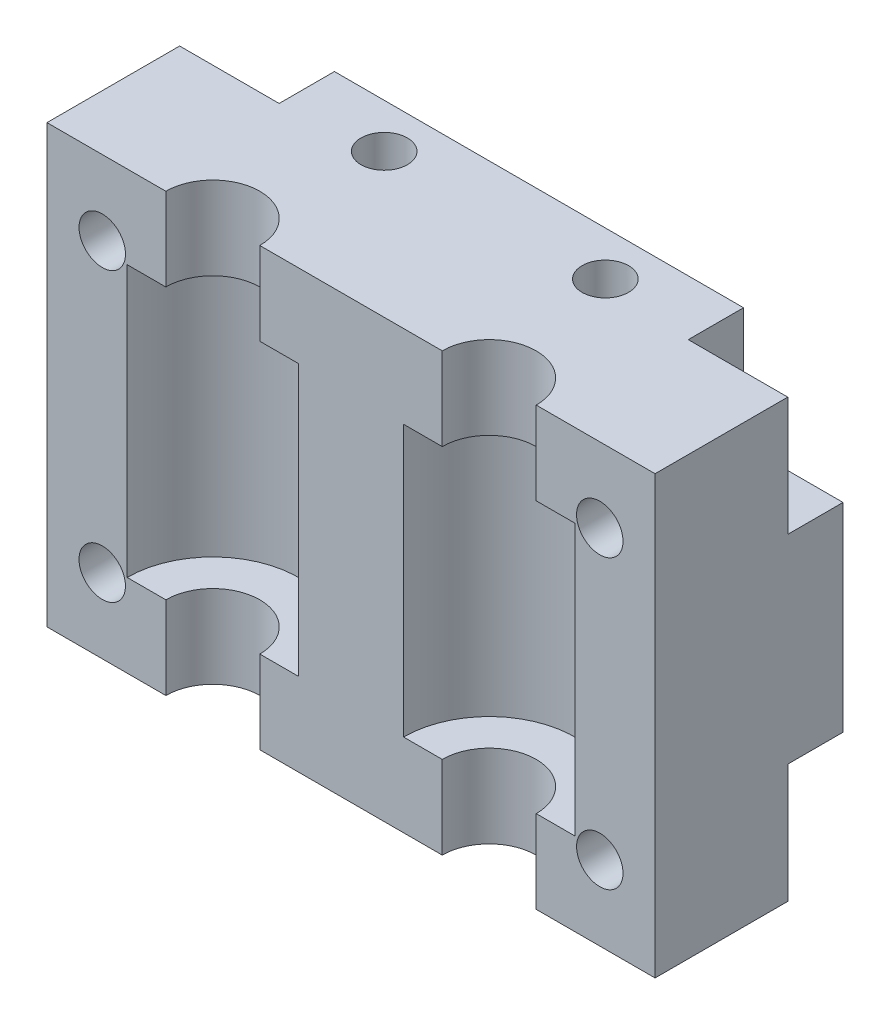
SolidWorks part; units mm, degrees
ref_plane "Plan de face" through (0, 0, 0) normal (0, 0, 1) x (1, 0, 0)
ref_plane "Plan de dessus" through (0, 0, 0) normal (0, 1, 0) x (1, 0, 0)
ref_plane "Plan de droite" through (0, 0, 0) normal (1, 0, 0) x (0, 0, -1)
sketch "Esquisse1" plane through (0, 0, 0) normal (0, 0, 1) x (1, 0, 0)
  line L1 (-27.5, -22.5) -> (27.5, -22.5)
  line L2 (-27.5, -22.5) -> (-27.5, 22.5)
  line L3 (-27.5, 22.5) -> (27.5, 22.5)
  line L4 (27.5, -22.5) -> (27.5, 22.5)
  line L5 (-27.5, -22.5) -> (27.5, 22.5) construction
  line L6 (-27.5, 22.5) -> (27.5, -22.5) construction
  point P0 (0, 0)
  dimension "D1" = 55
  dimension "D2" = 45
extrude "Boss.-Extru.1" add sketch "Esquisse1" along normal blind 12
sketch "Esquisse2" plane through (0, 22.5, 0) normal (0, 1, 0) x (1, 0, 0)
  line L0 (27.5, -12) -> (-27.5, -12) construction
  line L1 (-27.5, -12) -> (-27.5, 0) construction
  line L2 (27.5, -12) -> (27.5, 0) construction
  circle A0 centre (-12.5, -12) radius 4.25
  circle A1 centre (12.5, -12) radius 4.25
  dimension "D1" = 8.5
  dimension "D3" = 8.5
  dimension "D2" = 15
  dimension "D4" = 15
extrude "Enlèv. mat.-Extru.1" cut sketch "Esquisse2" against normal through all
sketch "Esquisse3" plane through (0, 0, 0) normal (0, 1, 0) x (1, 0, 0)
  circle A0 centre (-12.5, -12) radius 7.75
  dimension "D1" = 15.5
extrude "Enlèv. mat.-Extru.2" cut sketch "Esquisse3" against normal blind 12.25 and the other way blind 12.25
sketch "Esquisse9" plane through (0, 0, 12) normal (0, 0, 1) x (1, 0, 0)
  line L0 (-8.25, -22.5) -> (8.25, -22.5) construction
  line L1 (-30.9208, -30.2281) -> (30.1419, -30.2281)
  line L2 (-30.9208, -30.2281) -> (-30.9208, -18)
  line L3 (-30.9208, -18) -> (30.1419, -18)
  line L4 (30.1419, -30.2281) -> (30.1419, -18)
  line L5 (8.25, 22.5) -> (-8.25, 22.5) construction
  line L6 (31.3881, 26.1002) -> (-28.039, 26.1002)
  line L7 (31.3881, 26.1002) -> (31.3881, 18)
  line L8 (31.3881, 18) -> (-28.039, 18)
  line L9 (-28.039, 26.1002) -> (-28.039, 18)
  dimension "D1" = 4.5
  dimension "D2" = 4.5
extrude "Enlèv. mat.-Extru.7" cut sketch "Esquisse9" against normal blind 31
sketch "Sketch1" plane through (0, 0, 0) normal (0, 0, -1) x (-1, 0, 0)
  line L4 (-27.5, -18) -> (27.5, -18)
  line L5 (27.5, -18) -> (27.5, 18)
  line L6 (27.5, 18) -> (-27.5, 18)
  line L7 (-27.5, 18) -> (-27.5, -18)
  line L8 (-27.5, -18) -> (27.5, -18)
  line L9 (27.5, -18) -> (27.5, 18)
  line L10 (27.5, 18) -> (-27.5, 18)
  line L11 (-27.5, 18) -> (-27.5, -18)
  dimension "D1" = 0
extrude "Boss-Extrude1" add sketch "Sketch1" along normal blind 5
sketch "Sketch2" plane through (0, 0, 12) normal (0, 0, 1) x (1, 0, 0)
  line L0 (-27.5, 18) -> (-16.75, 18) construction
  line L1 (-27.5, 18) -> (-27.5, -18) construction
  line L2 (0, 18) -> (0, -18) construction
  line L3 (-8.25, 18) -> (8.25, 18) construction
  line L4 (8.25, -18) -> (-8.25, -18) construction
  line L5 (-27.5, 0) -> (27.5, 0) construction
  line L6 (27.5, -18) -> (27.5, 18) construction
  circle A0 centre (-22.5, 13) radius 2.1
  circle A1 centre (22.5, 13) radius 2.1
  circle A2 centre (22.5, -13) radius 2.1
  circle A3 centre (-22.5, -13) radius 2.1
  dimension "D1" = 4.2
  dimension "D2" = 5
  dimension "D3" = 5
extrude "Cut-Extrude1" cut sketch "Sketch2" against normal through all
sketch "Sketch3" plane through (0, 0, -5) normal (0, 0, -1) x (-1, 0, 0)
  circle A0 centre (-22.5, 13) radius 4
  circle A1 centre (22.5, 13) radius 4
  circle A2 centre (22.5, -13) radius 4
  circle A3 centre (-22.5, -13) radius 4
  dimension "D1" = 8
extrude "Cut-Extrude2" cut sketch "Sketch3" against normal blind 10
sketch "Sketch4" plane through (0, 0, -5) normal (0, 0, -1) x (-1, 0, 0)
  line L0 (-18.5, 13) -> (-18.5, 18)
  line L1 (-22.5, 9) -> (-27.5, 9)
  line L2 (-22.5, -9) -> (-27.5, -9)
  line L3 (-18.5, -13) -> (-18.5, -18)
  line L4 (-27.5, 18) -> (-27.5, -18)
  line L5 (-27.5, -18) -> (27.5, -18)
  line L6 (27.5, -18) -> (27.5, 18)
  line L7 (27.5, 18) -> (-27.5, 18)
  line L8 (-27.5, 18) -> (-27.5, 9)
  line L9 (-27.5, -18) -> (-18.5, -18)
  line L10 (27.5, -18) -> (27.5, -9)
  line L11 (27.5, 18) -> (18.5, 18)
  line L12 (18.5, -13) -> (18.5, -18)
  line L13 (22.5, -9) -> (27.5, -9)
  line L14 (22.5, 9) -> (27.5, 9)
  line L15 (18.5, 13) -> (18.5, 18)
  line L16 (-18.5, 18) -> (-27.5, 18)
  line L17 (-27.5, -9) -> (-27.5, -18)
  line L18 (18.5, -18) -> (27.5, -18)
  line L19 (27.5, 9) -> (27.5, 18)
  circle A0 centre (-22.5, 13) radius 4 construction
  circle A1 centre (-22.5, -13) radius 4 construction
  circle A2 centre (22.5, -13) radius 4 construction
  circle A3 centre (22.5, 13) radius 4 construction
  arc A4 (-18.5, 13) -> (-22.5, 9) centre (-22.5, 13) ccw
  arc A5 (-22.5, -9) -> (-18.5, -13) centre (-22.5, -13) ccw
  arc A6 (18.5, -13) -> (22.5, -9) centre (22.5, -13) ccw
  arc A7 (22.5, 9) -> (18.5, 13) centre (22.5, 13) ccw
  dimension "D1" = 0
extrude "Cut-Extrude3" cut sketch "Sketch4" against normal blind 5
sketch "Sketch5" plane through (0, 18, 0) normal (0, 1, 0) x (1, 0, 0)
  line L0 (-27.5, -12) -> (-27.5, 0) construction
  line L1 (27.5, 0) -> (27.5, 5) construction
  line L2 (-18.5, 5) -> (18.5, 5) construction
  circle A0 centre (-10, 1) radius 2.1
  circle A1 centre (10, 1) radius 2.1
  dimension "D1" = 4.2
  dimension "D2" = 4.2
  dimension "D3" = 17.5
  dimension "D4" = 17.5
  dimension "D5" = 4
  dimension "D6" = 4
extrude "Cut-Extrude4" cut sketch "Sketch5" against normal through all
sketch "Sketch7" plane through (0, 18, 0) normal (0, 1, 0) x (1, 0, 0)
  line L10 (18.5, 5) -> (-18.5, 5)
  line L11 (-18.5, 5) -> (-18.5, 0)
  line L12 (-18.5, 0) -> (-27.5, 0)
  line L13 (-27.5, 0) -> (-27.5, -12)
  line L14 (-27.5, -12) -> (-16.75, -12)
  line L15 (-8.25, -12) -> (8.25, -12)
  line L16 (16.75, -12) -> (27.5, -12)
  line L17 (27.5, -12) -> (27.5, 0)
  line L18 (27.5, 0) -> (18.5, 0)
  line L19 (18.5, 0) -> (18.5, 5)
  line L20 (18.5, 5) -> (-18.5, 5)
  line L21 (-18.5, 5) -> (-18.5, 0)
  line L22 (-18.5, 0) -> (-27.5, 0)
  line L23 (-27.5, 0) -> (-27.5, -12)
  line L24 (-27.5, -12) -> (-16.75, -12)
  line L25 (-8.25, -12) -> (8.25, -12)
  line L26 (16.75, -12) -> (27.5, -12)
  line L27 (27.5, -12) -> (27.5, 0)
  line L28 (27.5, 0) -> (18.5, 0)
  line L29 (18.5, 0) -> (18.5, 5)
  circle A0 centre (10, 1) radius 2.1 construction
  circle A1 centre (-10, 1) radius 2.1 construction
  arc A2 (-8.25, -12) -> (-16.75, -12) centre (-12.5, -12) ccw
  arc A3 (16.75, -12) -> (8.25, -12) centre (12.5, -12) ccw
  arc A4 (-8.25, -12) -> (-16.75, -12) centre (-12.5, -12) ccw
  arc A5 (16.75, -12) -> (8.25, -12) centre (12.5, -12) ccw
  circle A6 centre (10, 1) radius 2.1
  circle A7 centre (-10, 1) radius 2.1
  dimension "D1" = 0
extrude "Boss-Extrude4" add sketch "Sketch7" along normal blind 2
sketch "Sketch8" plane through (0, -18, 0) normal (0, -1, 0) x (1, 0, 0)
  line L10 (-27.5, 0) -> (-18.5, 0)
  line L11 (-18.5, 0) -> (-18.5, -5)
  line L12 (-18.5, -5) -> (18.5, -5)
  line L13 (18.5, -5) -> (18.5, 0)
  line L14 (18.5, 0) -> (27.5, 0)
  line L15 (27.5, 0) -> (27.5, 12)
  line L16 (27.5, 12) -> (16.75, 12)
  line L17 (8.25, 12) -> (-8.25, 12)
  line L18 (-16.75, 12) -> (-27.5, 12)
  line L19 (-27.5, 12) -> (-27.5, 0)
  line L20 (-27.5, 0) -> (-18.5, 0)
  line L21 (-18.5, 0) -> (-18.5, -5)
  line L22 (-18.5, -5) -> (18.5, -5)
  line L23 (18.5, -5) -> (18.5, 0)
  line L24 (18.5, 0) -> (27.5, 0)
  line L25 (27.5, 0) -> (27.5, 12)
  line L26 (27.5, 12) -> (16.75, 12)
  line L27 (8.25, 12) -> (-8.25, 12)
  line L28 (-16.75, 12) -> (-27.5, 12)
  line L29 (-27.5, 12) -> (-27.5, 0)
  circle A0 centre (-10, -1) radius 2.1 construction
  circle A1 centre (10, -1) radius 2.1 construction
  arc A2 (8.25, 12) -> (16.75, 12) centre (12.5, 12) ccw
  arc A3 (-16.75, 12) -> (-8.25, 12) centre (-12.5, 12) ccw
  arc A4 (8.25, 12) -> (16.75, 12) centre (12.5, 12) ccw
  arc A5 (-16.75, 12) -> (-8.25, 12) centre (-12.5, 12) ccw
  circle A6 centre (10, -1) radius 2.1
  circle A7 centre (-10, -1) radius 2.1
  dimension "D1" = 0
extrude "Boss-Extrude5" add sketch "Sketch8" along normal blind 2
sketch "Sketch9" plane through (0, 0, -5) normal (0, 0, -1) x (-1, 0, 0)
  line L0 (-27.5, 20) -> (-27.5, 9) construction
  line L1 (-13.5, 16) -> (-6.5, 16)
  line L2 (-13.5, 16) -> (-13.5, 12.8)
  line L3 (-13.5, 12.8) -> (-6.5, 12.8)
  line L4 (-6.5, 16) -> (-6.5, 12.8)
  line L5 (-18.5, 20) -> (18.5, 20) construction
  line L6 (0, 20) -> (0, -9.1772) construction
  line L7 (13.5, 12.8) -> (6.5, 12.8)
  line L8 (6.5, 16) -> (6.5, 12.8)
  line L9 (13.5, 16) -> (6.5, 16)
  line L10 (13.5, 16) -> (13.5, 12.8)
  line L11 (-27.5, 0) -> (-8.3783, 0) construction
  line L12 (-27.5, 9) -> (-27.5, -9) construction
  line L13 (13.5, -16) -> (13.5, -12.8)
  line L14 (13.5, -16) -> (6.5, -16)
  line L15 (6.5, -16) -> (6.5, -12.8)
  line L16 (13.5, -12.8) -> (6.5, -12.8)
  line L17 (-13.5, -12.8) -> (-6.5, -12.8)
  line L18 (-6.5, -16) -> (-6.5, -12.8)
  line L19 (-13.5, -16) -> (-6.5, -16)
  line L20 (-13.5, -16) -> (-13.5, -12.8)
  point P4 (-10, 16)
  dimension "D1" = 7
  dimension "D2" = 17.5
  dimension "D3" = 4
  dimension "D4" = 3.2
extrude "Cut-Extrude6" cut sketch "Sketch9" against normal blind 8
ref_plane "Plane1" through (0, 0, 0) normal (-1, 0, 0) x (0, 0, 1)
mirror "Mirror1" about plane through (0, 0, 0) normal (-1, 0, 0) of "Enlèv. mat.-Extru.2"
sketch "Sketch10" plane through (0, -20, 0) normal (0, -1, 0) x (1, 0, 0)
  line L10 (-27.5, 12) -> (-27.5, 0)
  line L11 (-27.5, 0) -> (-18.5, 0)
  line L12 (-18.5, 0) -> (-18.5, -5)
  line L13 (-18.5, -5) -> (18.5, -5)
  line L14 (18.5, -5) -> (18.5, 0)
  line L15 (18.5, 0) -> (27.5, 0)
  line L16 (27.5, 0) -> (27.5, 12)
  line L17 (27.5, 12) -> (16.75, 12)
  line L18 (8.25, 12) -> (-8.25, 12)
  line L19 (-16.75, 12) -> (-27.5, 12)
  line L20 (-27.5, 12) -> (-27.5, 0)
  line L21 (-27.5, 0) -> (-18.5, 0)
  line L22 (-18.5, 0) -> (-18.5, -5)
  line L23 (-18.5, -5) -> (18.5, -5)
  line L24 (18.5, -5) -> (18.5, 0)
  line L25 (18.5, 0) -> (27.5, 0)
  line L26 (27.5, 0) -> (27.5, 12)
  line L27 (27.5, 12) -> (16.75, 12)
  line L28 (8.25, 12) -> (-8.25, 12)
  line L29 (-16.75, 12) -> (-27.5, 12)
  arc A2 (8.25, 12) -> (16.75, 12) centre (12.5, 12) ccw
  arc A3 (-16.75, 12) -> (-8.25, 12) centre (-12.5, 12) ccw
  arc A4 (8.25, 12) -> (16.75, 12) centre (12.5, 12) ccw
  arc A5 (-16.75, 12) -> (-8.25, 12) centre (-12.5, 12) ccw
  dimension "D1" = 0
extrude "Cut-Extrude7" cut sketch "Sketch10" against normal blind 0.25
sketch "Sketch11" plane through (0, 20, 0) normal (0, 1, 0) x (1, 0, 0)
  line L10 (18.5, 0) -> (18.5, 5)
  line L11 (18.5, 5) -> (-18.5, 5)
  line L12 (-18.5, 5) -> (-18.5, 0)
  line L13 (-18.5, 0) -> (-27.5, 0)
  line L14 (-27.5, 0) -> (-27.5, -12)
  line L15 (-27.5, -12) -> (-16.75, -12)
  line L16 (-8.25, -12) -> (8.25, -12)
  line L17 (16.75, -12) -> (27.5, -12)
  line L18 (27.5, -12) -> (27.5, 0)
  line L19 (27.5, 0) -> (18.5, 0)
  line L20 (18.5, 0) -> (18.5, 5)
  line L21 (18.5, 5) -> (-18.5, 5)
  line L22 (-18.5, 5) -> (-18.5, 0)
  line L23 (-18.5, 0) -> (-27.5, 0)
  line L24 (-27.5, 0) -> (-27.5, -12)
  line L25 (-27.5, -12) -> (-16.75, -12)
  line L26 (-8.25, -12) -> (8.25, -12)
  line L27 (16.75, -12) -> (27.5, -12)
  line L28 (27.5, -12) -> (27.5, 0)
  line L29 (27.5, 0) -> (18.5, 0)
  arc A2 (-8.25, -12) -> (-16.75, -12) centre (-12.5, -12) ccw
  arc A3 (16.75, -12) -> (8.25, -12) centre (12.5, -12) ccw
  arc A4 (-8.25, -12) -> (-16.75, -12) centre (-12.5, -12) ccw
  arc A5 (16.75, -12) -> (8.25, -12) centre (12.5, -12) ccw
  dimension "D1" = 0
extrude "Cut-Extrude8" cut sketch "Sketch11" against normal blind 0.25
move or copy body "Body-Move/Copy1" [suppressed] bodies to move or copy 135
